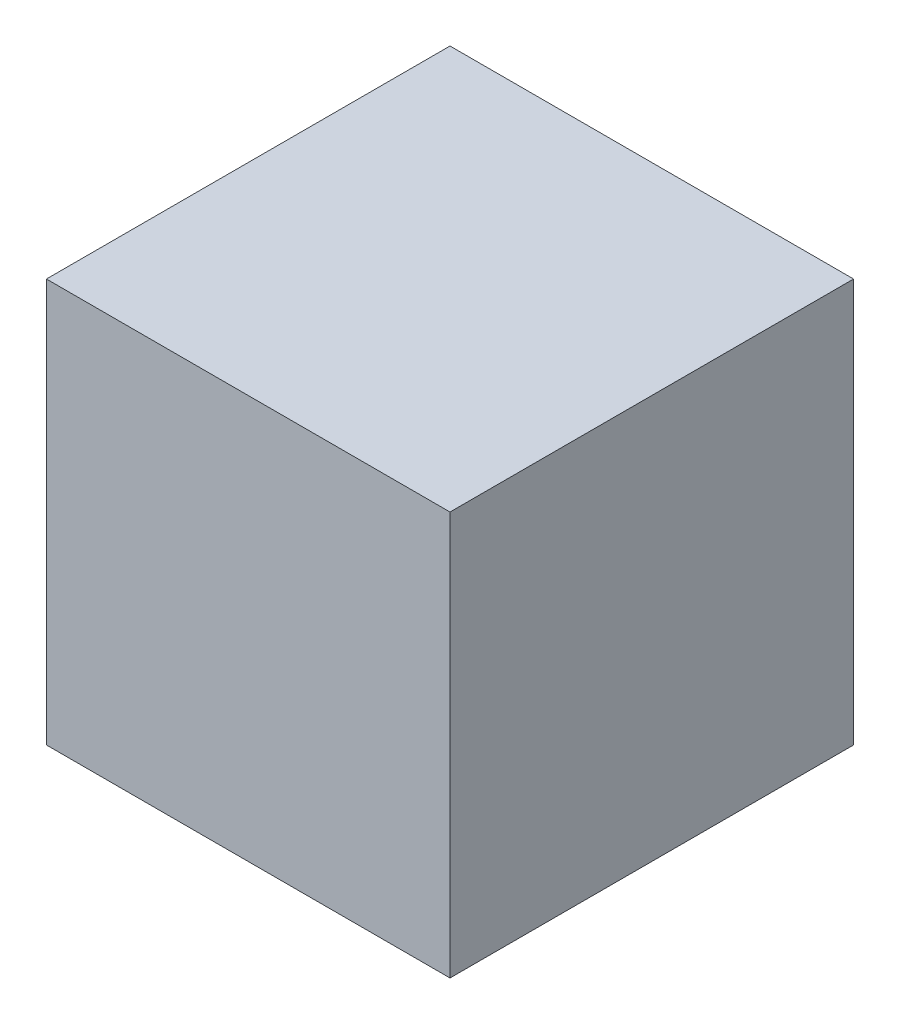
SolidWorks part; units mm, degrees
ref_plane "前视基准面" through (0, 0, 0) normal (0, 0, 1) x (1, 0, 0)
ref_plane "上视基准面" through (0, 0, 0) normal (0, 1, 0) x (1, 0, 0)
ref_plane "右视基准面" through (0, 0, 0) normal (1, 0, 0) x (0, 0, -1)
other "Configuration Table"
sketch "草图1" plane through (0, 0, 0) normal (0, 0, 1) x (1, 0, 0)
  line L1 (-50, -50) -> (50, -50)
  line L2 (-50, -50) -> (-50, 50)
  line L3 (-50, 50) -> (50, 50)
  line L4 (50, -50) -> (50, 50)
  line L5 (-50, -50) -> (50, 50) construction
  line L6 (-50, 50) -> (50, -50) construction
  point P0 (0, 0)
  point P6 (0, -50)
  dimension "D1" = 100
  dimension "D2" = 100
extrude "凸台-拉伸1" add sketch "草图1" along normal blind 100
